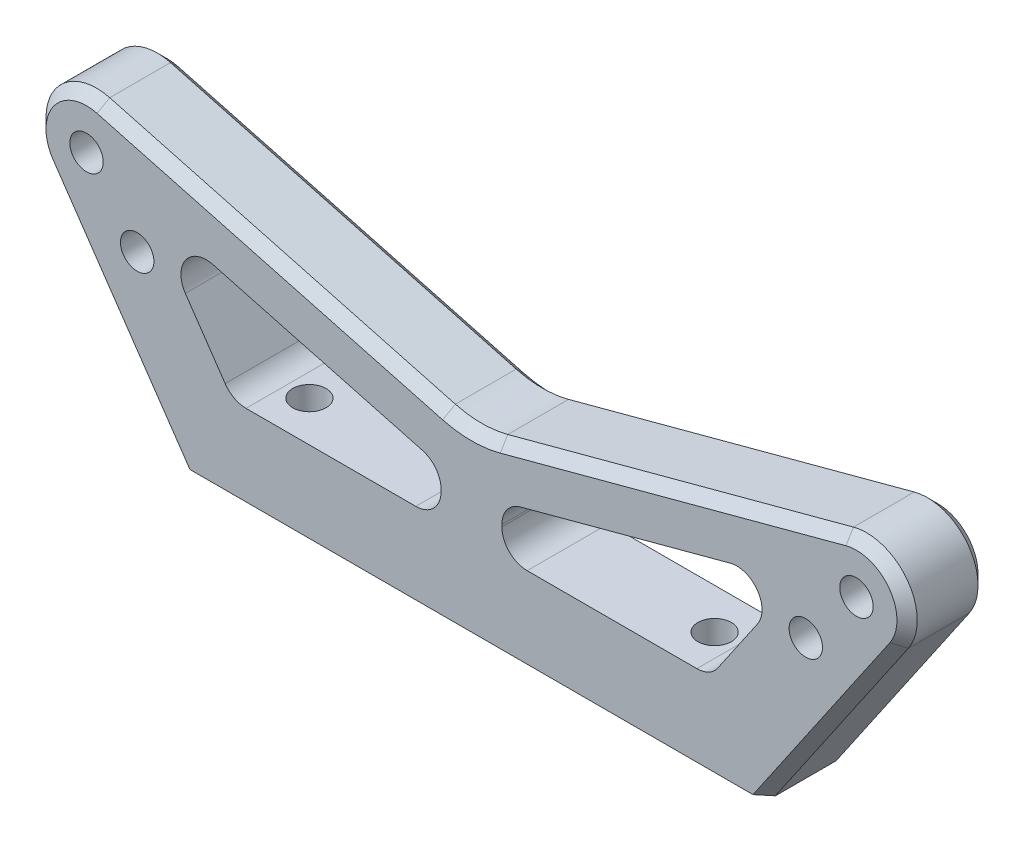
SolidWorks part; units mm, degrees
material "3.1325 (EN-AW 2017A)"
ref_plane "Plan de face" through (0, 0, 0) normal (0, 0, 1) x (1, 0, 0)
ref_plane "Plan de dessus" through (0, 0, 0) normal (0, 1, 0) x (1, 0, 0)
ref_plane "Plan de droite" through (0, 0, 0) normal (1, 0, 0) x (0, 0, -1)
sketch "Esquisse1" plane through (0, 0, 0) normal (0, 0, 1) x (1, 0, 0)
  line L0 (-29, 0) -> (29, 0)
  line L1 (29, 0) -> (42.126, 19.1757)
  line L3 (-42.126, 19.1757) -> (-29, 0)
  line L4 (0, 0) -> (0, 28) construction
  line L5 (-121.1128, -90.5) -> (52.6461, -90.5)
  line L6 (-36.7059, 26.8296) -> (0, 16.9943)
  line L7 (0, 16.9943) -> (36.7059, 26.8296)
  line L8 (-117.0312, -48.5) -> (-33, 16) construction
  line L9 (-117.0312, -48.5) -> (-38, 22) construction
  line L10 (-117.0312, -48.5) -> (-37, 25.5) construction
  arc A0 (42.126, 19.1757) -> (36.7059, 26.8296) centre (38, 22) ccw
  arc A1 (-36.7059, 26.8296) -> (-42.126, 19.1757) centre (-38, 22) ccw
  point P11 (-37, 25.5)
  point P12 (-117.0312, -48.5)
  point P15 (-33, 16)
  point P16 (33, 16)
  dimension "D2" = 5
  dimension "D1" = 58
  dimension "D3" = 76
  dimension "D4" = 22
  dimension "D5" = 25.5
  dimension "D6" = 37
  dimension "D7" = 116
  dimension "D8" = 42
  dimension "D9" = 109
  dimension "D10" = 105.9065
  dimension "D11" = 66
  dimension "D12" = 16
  dimension "D13" = 105.9316
  dimension "D14" = 15
  dimension "D15" = 42.758
  dimension "D16" = 41.735
  dimension "D17" = 37.509
extrude "Boss.-Extru.1" add sketch "Esquisse1" along normal mid plane 8
hole_wizard "Trou taraudé M42" positions "Esquisse3" profile "Esquisse4" tap size "M4" standard "ISO" end condition through all
sketch "Esquisse3" plane through (0, 0, 4) normal (0, 0, 1) x (1, 0, 0)
  point P0 (-38, 22)
  point P3 (38, 22)
  point P6 (-33, 16)
  point P9 (33, 16)
sketch "Esquisse4" plane through (-38, 22, 4) normal (1, 0, 0) x (0, -1, 0)
  line L0 (0, 0) -> (0, 8)
  line L1 (0, 8) -> (1.65, 8)
  line L2 (1.65, 8) -> (1.65, 0)
  line L5 (1.65, 0) -> (0, 0)
  line L11 (0, -6.35) -> (0, 107.95) construction
  dimension "Diamètre du trou pour taraudage jusqu'au prochain" = 3.3
  dimension "Profondeur du trou pour taraudage jusqu'au prochain" = 8
cosmetic thread "Filetage de perçage10" parameters "D2"=4
cosmetic thread "Filetage de perçage11" parameters "D2"=4
cosmetic thread "Filetage de perçage12" parameters "D2"=4
cosmetic thread "Filetage de perçage13" parameters "D2"=4
hole_wizard "Trou taraudé M43" positions "Esquisse5" profile "Esquisse6" tap size "M4" standard "ISO"
sketch "Esquisse5" plane through (0, 0, 0) normal (0, -1, 0) x (-1, 0, 0)
  point P0 (20, 0)
  point P2 (-20, 0)
  point P8 (0, -0.5)
  dimension "D1" = 40
  dimension "D2" = 20
  dimension "D3" = 0.5
sketch "Esquisse6" plane through (-20, 0, 0) normal (1, 0, 0) x (0, 0, -1)
  line L0 (0, 0) -> (0, 16.4914)
  line L1 (0, 16.4914) -> (1.65, 15.5)
  line L2 (1.65, 15.5) -> (1.65, 0)
  line L5 (1.65, 0) -> (0, 0)
  line L10 (0, 16.4914) -> (-1.65, 15.5) construction
  line L11 (0, -6.35) -> (0, 107.95) construction
  dimension "Diamètre du trou pour taraudage" = 3.3
  dimension "Profondeur du trou pour taraudage" = 15.5
  dimension "Angle de pointe" = 118
cosmetic thread "Filetage de perçage14" parameters "D1"=12, "D2"=4
cosmetic thread "Filetage de perçage15" parameters "D1"=12, "D2"=4
cosmetic thread "Filetage de perçage16" parameters "D1"=12, "D2"=4
fillet "Congé1" radius 10 1 edges at (0, 16.9943, 0)
sketch "Esquisse8" plane through (0, 0, 4) normal (0, 0, 1) x (1, 0, 0)
  line L0 (-3, 10.7035) -> (-3, 10.5)
  line L1 (-5.5, 8) -> (-22.2512, 8)
  line L2 (-24.3142, 9.0879) -> (-28.2472, 14.8337)
  line L3 (-25.5372, 18.6606) -> (-4.853, 13.1183)
  line L4 (-36.7059, 26.8296) -> (-2.5882, 17.6878) construction
  line L5 (-42.126, 19.1757) -> (-29, 0) construction
  line L6 (-29, 0) -> (29, 0) construction
  arc A0 (-22.2512, 8) -> (-24.3142, 9.0879) centre (-22.2512, 10.5) cw
  arc A1 (-3, 10.5) -> (-5.5, 8) centre (-5.5, 10.5) cw
  arc A2 (-3, 10.7035) -> (-4.853, 13.1183) centre (-5.5, 10.7035) ccw
  arc A3 (-28.2472, 14.8337) -> (-25.5372, 18.6606) centre (-26.1842, 16.2458) cw
  dimension "D5" = 2.5
  dimension "D1" = 3
  dimension "D2" = 8
  dimension "D3" = 5
  dimension "D4" = 9
extrude "Enlèv. mat.-Extru.1" cut sketch "Esquisse8" against normal through all both and the other way through all
mirror "Symétrie1" about plane through (0, 0, 0) normal (1, 0, 0) of "Enlèv. mat.-Extru.1"
chamfer "Chanfrein1" distance 1 angle 45 14 edges at (-35.563, 9.5879, -4) (-35.563, 9.5879, 4) (-42.0805, 24.8896, -4) (-42.0805, 24.8896, 4) (-19.647, 22.2587, 4) (-19.647, 22.2587, -4) (0, 17.3471, 4) (0, 17.3471, -4) (19.647, 22.2587, -4) (19.647, 22.2587, 4) (42.0805, 24.8896, -4) (42.0805, 24.8896, 4) (35.563, 9.5879, -4) (35.563, 9.5879, 4)
